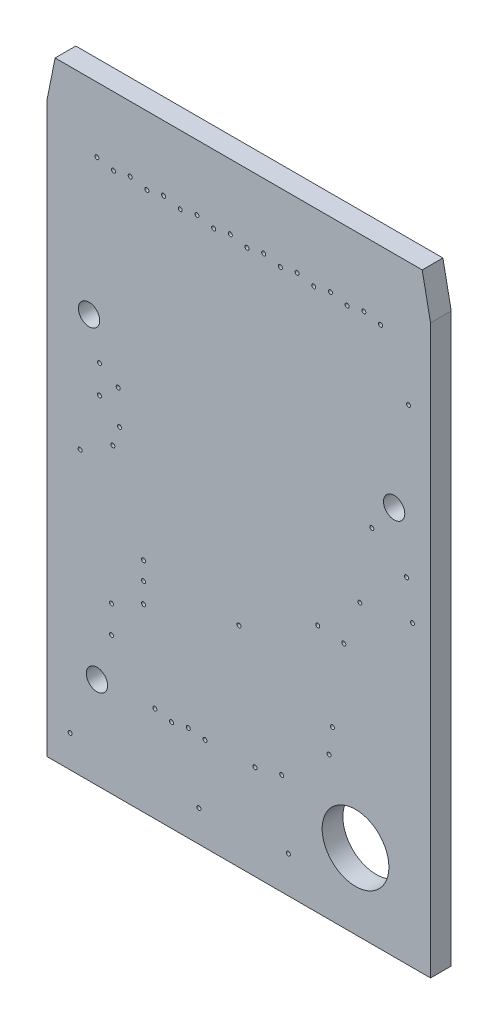
SolidWorks part; units mm, degrees
ref_plane "Front Plane" through (0, 0, 0) normal (0, 0, 1) x (1, 0, 0)
ref_plane "Top Plane" through (0, 0, 0) normal (0, 1, 0) x (1, 0, 0)
ref_plane "Right Plane" through (0, 0, 0) normal (1, 0, 0) x (0, 0, -1)
ref_plane "Dielectric_Layer Layer 1" through (0, 0, 0.7874) normal (0, 0, 1) x (1, 0, 0)
sketch "Sketch1" plane through (0, 0, 0) normal (0, 0, 1) x (1, 0, 0)
  line L0 (14.605, 0) -> (0, 0)
  line L1 (0, 0) -> (0, 21.59)
  line L2 (0, 21.59) -> (0.3175, 23.1775)
  line L3 (0.3175, 23.1775) -> (14.2875, 23.1775)
  line L4 (14.2875, 23.1775) -> (14.605, 21.59)
  line L5 (14.605, 21.59) -> (14.605, 0)
extrude "Board_Outline" add sketch "Sketch1" along normal blind 0.7874 separate body
sketch "Sketch2" plane through (0, 0, 0) normal (0, 0, 1) x (1, 0, 0)
  circle A0 centre (2.4638, 6.2738) radius 0.0762
  circle A1 centre (7.9248, 3.6068) radius 0.0762
  circle A2 centre (11.303, 9.3726) radius 0.0762
  circle A3 centre (10.3124, 9.4742) radius 0.0762
  circle A4 centre (13.7668, 18.4658) radius 0.0762
  circle A5 centre (1.27, 10.7442) radius 0.0762
  circle A6 centre (1.905, 20.701) radius 0.0762
  circle A7 centre (2.5146, 11.5062) radius 0.0762
  circle A8 centre (11.9126, 11.0236) radius 0.0762
  circle A9 centre (11.43, 20.574) radius 0.0762
  circle A10 centre (10.795, 20.701) radius 0.0762
  circle A11 centre (4.1148, 3.6322) radius 0.0762
  circle A12 centre (8.9408, 3.8608) radius 0.0762
  circle A13 centre (3.683, 8.3058) radius 0.0762
  circle A14 centre (4.7498, 3.5052) radius 0.0762
  circle A15 centre (12.065, 20.701) radius 0.0762
  circle A16 centre (10.16, 20.574) radius 0.0762
  circle A17 centre (9.525, 20.701) radius 0.0762
  circle A18 centre (8.89, 20.574) radius 0.0762
  circle A19 centre (10.7442, 5.4356) radius 0.0762
  circle A20 centre (3.683, 7.62) radius 0.0762
  circle A21 centre (9.1948, 1.397) radius 0.0762
  circle A22 centre (3.683, 6.858) radius 0.0762
  circle A23 centre (7.3152, 7.9756) radius 0.0762
  circle A24 centre (6.0198, 3.556) radius 0.0762
  circle A25 centre (5.3848, 3.6322) radius 0.0762
  circle A26 centre (8.255, 20.701) radius 0.0762
  circle A27 centre (7.62, 20.574) radius 0.0762
  circle A28 centre (6.985, 20.701) radius 0.0762
  circle A29 centre (6.35, 20.574) radius 0.0762
  circle A30 centre (5.715, 20.701) radius 0.0762
  circle A31 centre (5.08, 20.574) radius 0.0762
  circle A32 centre (4.445, 20.701) radius 0.0762
  circle A33 centre (3.81, 20.574) radius 0.0762
  circle A34 centre (3.175, 20.701) radius 0.0762
  circle A35 centre (2.54, 20.574) radius 0.0762
  circle A36 centre (2.0066, 13.97) radius 0.0762
  circle A37 centre (12.7, 20.574) radius 0.0762
  circle A38 centre (0.889, 1.2192) radius 0.0762
  circle A39 centre (13.6906, 12.7508) radius 0.0762
  circle A40 centre (2.0066, 12.9032) radius 0.0762
  circle A41 centre (12.3698, 13.716) radius 0.0762
  circle A42 centre (5.7912, 1.1938) radius 0.0762
  circle A43 centre (2.4638, 5.2324) radius 0.0762
  circle A44 centre (2.7178, 13.5128) radius 0.0762
  circle A45 centre (10.8712, 6.4008) radius 0.0762
  circle A46 centre (13.9192, 11.3538) radius 0.0762
  circle A47 centre (2.7686, 12.2428) radius 0.0762
extrude "NPTH" cut sketch "Sketch2" along normal through all
sketch "Sketch3" plane through (0, 0, 0) normal (0, 0, 1) x (1, 0, 0)
  circle A0 centre (1.61, 15.37) radius 0.405
  circle A1 centre (11.75, 2.86) radius 1.27
  circle A2 centre (13.22, 14.81) radius 0.405
  circle A3 centre (1.91, 3.49) radius 0.405
extrude "PTH" cut sketch "Sketch3" along normal through all
